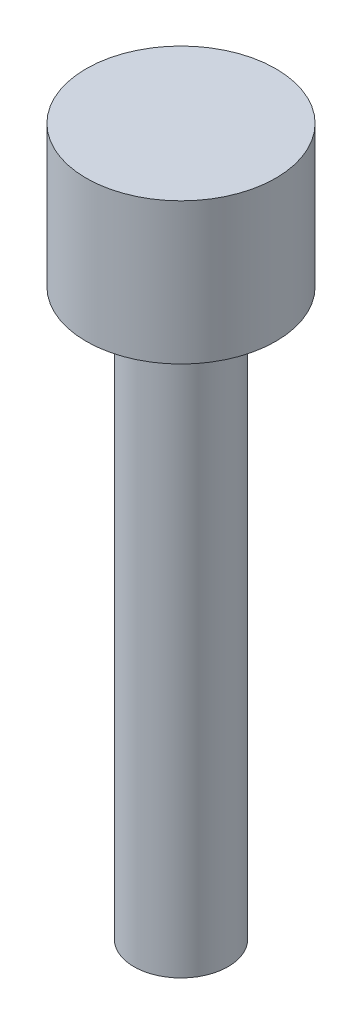
SolidWorks part; units mm, degrees
ref_plane "Front Plane" through (0, 0, 0) normal (0, 0, 1) x (1, 0, 0)
ref_plane "Top Plane" through (0, 0, 0) normal (0, 1, 0) x (1, 0, 0)
ref_plane "Right Plane" through (0, 0, 0) normal (1, 0, 0) x (0, 0, -1)
sketch "Sketch1" plane through (0, 0, 0) normal (0, 0, 1) x (1, 0, 0)
  line L0 (0, 0) -> (0, 15)
  line L1 (0, 15) -> (2.0126, 15)
  line L2 (2.0126, 15) -> (2.0126, 12)
  line L3 (2.0126, 12) -> (1, 12)
  line L4 (1, 12) -> (1, 0)
  line L5 (1, 0) -> (0, 0)
  dimension "D1" = 1
  dimension "D2" = 15
  dimension "D3" = 3
revolve "Revolve1" add sketch "Sketch1" angle 360 about L0
